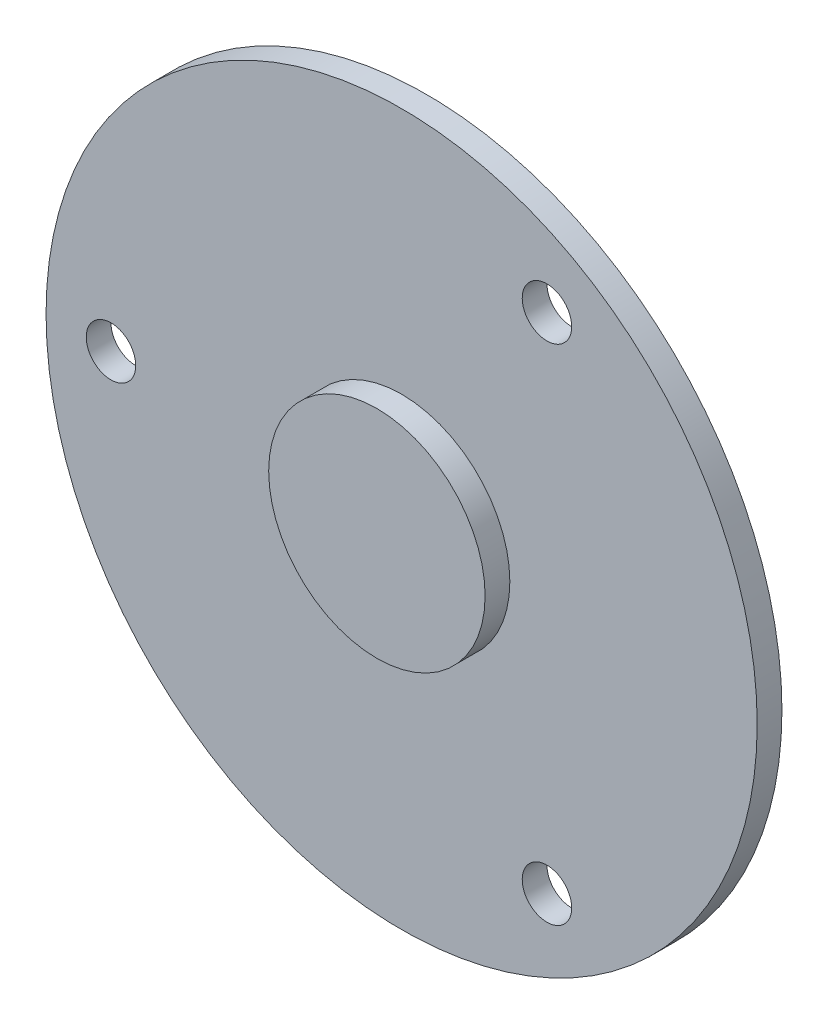
SolidWorks part; units mm, degrees
ref_plane "前视基准面" through (0, 0, 0) normal (0, 0, 1) x (1, 0, 0)
ref_plane "上视基准面" through (0, 0, 0) normal (0, 1, 0) x (1, 0, 0)
ref_plane "右视基准面" through (0, 0, 0) normal (1, 0, 0) x (0, 0, -1)
sketch "草图1" plane through (0, 0, 0) normal (0, 0, 1) x (1, 0, 0)
  circle A0 centre (0, 0) radius 57.5
  dimension "D1" = 115
extrude "凸台-拉伸1" add sketch "草图1" along normal blind 4
sketch "草图2" plane through (0, 0, 4) normal (0, 0, 1) x (1, 0, 0)
  circle A0 centre (0, 0) radius 17.5
  dimension "D1" = 35
extrude "凸台-拉伸2" add sketch "草图2" along normal blind 4
sketch "草图3" plane through (0, 0, 0) normal (0, 0, -1) x (-1, 0, 0)
  circle A0 centre (0, 0) radius 47 construction
  circle A1 centre (47, 0) radius 4
  dimension "D1" = 94
  dimension "D2" = 8
extrude "切除-拉伸1" cut sketch "草图3" against normal blind 12
pattern_circular "阵列(圆周)1" count 3 over 360 about axis through (0, 0, 0) along (0, 0, 1) of "切除-拉伸1"
